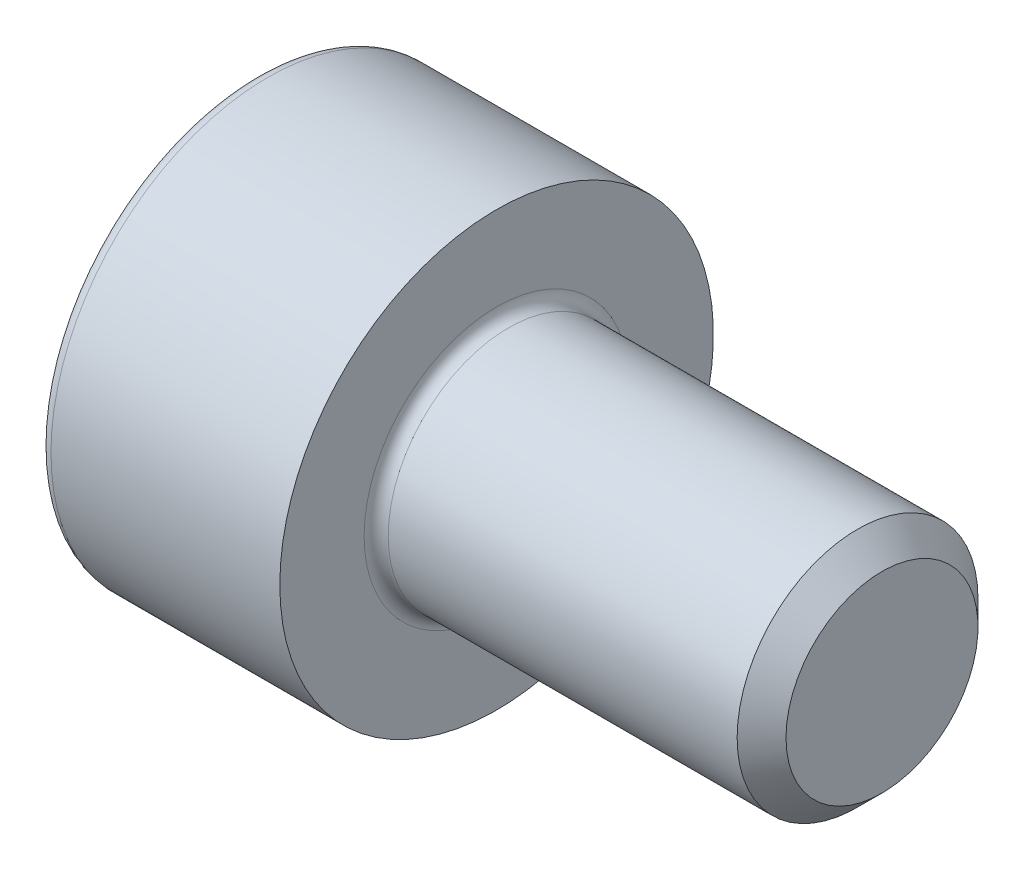
SolidWorks part; units mm, degrees
ref_plane "Front" through (0, 0, 0) normal (0, 0, 1) x (1, 0, 0)
ref_plane "Top" through (0, 0, 0) normal (0, 1, 0) x (1, 0, 0)
ref_plane "Right" through (0, 0, 0) normal (1, 0, 0) x (0, 0, -1)
sketch "Sketch1" plane through (0, 0, 0) normal (0, 0, 1) x (1, 0, 0)
  line L0 (3.7465, 1.25) -> (0.125, 1.25)
  line L1 (-2.5, 2.125) -> (-2.5, 0)
  line L2 (0, 2.25) -> (-2.375, 2.25)
  line L3 (0, 1.375) -> (0, 2.25)
  line L4 (4, 0.9965) -> (4, 0)
  line L5 (4, 0.9965) -> (3.7465, 1.25)
  line L6 (-2.5, 0) -> (0, 0) construction
  line L7 (-2.5, 0) -> (4, 0)
  arc A0 (-2.375, 2.25) -> (-2.5, 2.125) centre (-2.375, 2.125) ccw
  arc A1 (0, 1.375) -> (0.125, 1.25) centre (0.125, 1.375) ccw
  point P12 (0, 1.8125)
  dimension "D5" = 0.125
  dimension "D1" = 2.5
  dimension "D2" = 4.5
  dimension "D3" = 135
  dimension "D4" = 0.3585
  dimension "D6" = 4
  dimension "D7" = 2.5
revolve "Revolve1" add sketch "Sketch1" angle 360 about L7
sketch "Sketch2" plane through (-2.5, 0, 0) normal (-1, 0, 0) x (0, 0, 1)
  line L7 (1.025, 0.5918) -> (0, 1.1836)
  line L8 (0, 1.1836) -> (-1.025, 0.5918)
  line L9 (-1.025, 0.5918) -> (-1.025, -0.5918)
  line L10 (-1.025, -0.5918) -> (0, -1.1836)
  line L11 (0, -1.1836) -> (1.025, -0.5918)
  line L12 (1.025, -0.5918) -> (1.025, 0.5918)
  circle A0 centre (0, 0) radius 1.025 construction
  dimension "D1" = 2.05
extrude "Cut-Extrude1" cut sketch "Sketch2" against normal blind 1.1
